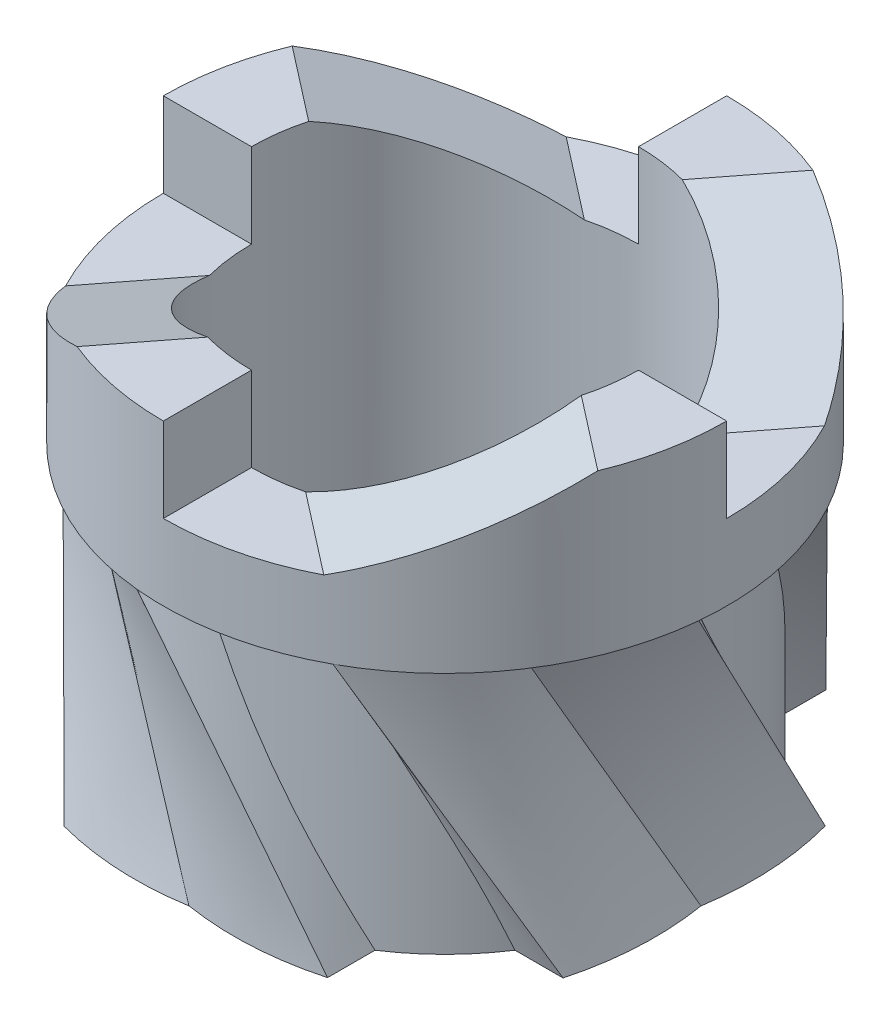
SolidWorks part; units mm, degrees
material "201.0-T43 Insulated Mold Casting (SS)"
ref_plane "Front Plane" through (0, 0, 0) normal (0, 0, 1) x (1, 0, 0)
ref_plane "Top Plane" through (0, 0, 0) normal (0, 1, 0) x (1, 0, 0)
ref_plane "Right Plane" through (0, 0, 0) normal (1, 0, 0) x (0, 0, -1)
sketch "Sketch1" plane through (0, 0, 0) normal (0, 1, 0) x (1, 0, 0)
  circle A0 centre (0, 0) radius 15
  dimension "D1" = 30
extrude "Boss-Extrude1" add sketch "Sketch1" along normal blind 17
sketch "Sketch2" plane through (0, 0, 0) normal (0, -1, 0) x (1, 0, 0)
  line L2 (8.1969, 15.5233) -> (8.1969, 12.5623)
  line L3 (-8.1969, 12.5623) -> (8.1969, 12.5623)
  line L15 (-8.1969, 12.5623) -> (-8.1969, 15.5623)
  arc A12 (8.1969, 15.5233) -> (0, 15.9711) centre (3.0626, -3.2123) ccw
  arc A13 (-8.1969, 15.5623) -> (0, 15.9711) centre (-3.1525, -3.1978) cw
  dimension "D1" = 3
ref_plane "Plane1" through (0, 8.5, 0) normal (0, 1, 0) x (1, 0, 0)
sketch "Sketch7" plane through (0, 17, 0) normal (0, 1, 0) x (1, 0, 0)
  line L3 (-15.4192, -8.4292) -> (-13.7853, -5.9132)
  line L4 (-13.7853, -5.9132) -> (-0.0367, -15)
  line L5 (-0.0367, -15) -> (-1.6706, -17.516)
  arc A2 (-8.7674, -13.2365) -> (-1.6706, -17.516) centre (4.5819, 0.8768) ccw
  arc A3 (-15.4192, -8.4292) -> (-8.7674, -13.2365) centre (-0.9711, 4.5569) ccw
  circle A4 centre (0, 0) radius 15 construction
  point P22 (0, 0)
  dimension "D1" = 3
  dimension "D2" = 3
loft "Loft3" add profiles "Sketch7", "Sketch2"
pattern_circular "CirPattern1" count 4 over 360 of "Loft3"
sketch "Sketch8" plane through (0, 17, 0) normal (0, 1, 0) x (1, 0, 0)
  line L0 (0, 0) -> (17.5728, 0) construction
  line L1 (17.5728, 0) -> (12.0728, 0)
  line L2 (0, -17.5728) -> (0, -12.0728)
  arc A0 (0, -17.5728) -> (17.5728, 0) centre (0, 0) ccw
  arc A1 (12.0728, 0) -> (0, -12.0728) centre (0, 0) cw
extrude "Boss-Extrude3" add sketch "Sketch8" along normal blind 10
ref_plane "Plane3" through (8.7864, 0, 8.7864) normal (-0.7071, 0, -0.7071) x (-0.7071, 0, 0.7071)
ref_plane "Plane4" through (0, 0, 0) normal (-1, 0, 0) x (0, 0, 1)
sketch "Sketch12" plane through (0, 0, 0) normal (-1, 0, 0) x (0, 0, 1)
  line L0 (15, 17) -> (15, 21.7329) construction
  line L2 (7.9763, 21.7329) -> (22.0237, 21.7329)
  line L3 (7.9763, 21.7329) -> (7.9763, 31.6878)
  line L4 (7.9763, 31.6878) -> (22.0237, 31.6878)
  line L5 (22.0237, 21.7329) -> (22.0237, 31.6878)
  point P7 (15, 21.7329)
extrude "Cut-Extrude2" cut sketch "Sketch12" against normal blind 3
ref_plane "Plane6" through (7.5364, 0, 5.8471) normal (-0.7901, 0, -0.613) x (-0.613, 0, 0.7901)
sketch "Sketch13" plane through (7.5364, 0, 5.8471) normal (-0.7901, 0, -0.613) x (-0.613, 0, 0.7901)
  line L0 (-4.6555, 27) -> (7.4005, 21.7329)
  line L1 (7.4005, 27) -> (-7.4005, 27) construction
  line L2 (7.4005, 21.7329) -> (11.8414, 21.7329)
  line L3 (11.8414, 21.7329) -> (11.8414, 27)
  line L4 (11.8414, 27) -> (-4.6555, 27)
extrude "Cut-Extrude3" cut sketch "Sketch13" against normal blind 9
pattern_circular "CirPattern11" count 4 over 360 about axis through (0, 0, 0) along (0, 1, 0) of "Boss-Extrude3", "Cut-Extrude2", "Cut-Extrude3"
sketch "Sketch14" plane through (0, 17, 0) normal (0, 1, 0) x (1, 0, 0)
  circle A0 centre (0, 0) radius 12.0728
extrude "Cut-Extrude4" cut sketch "Sketch14" against normal blind 24
